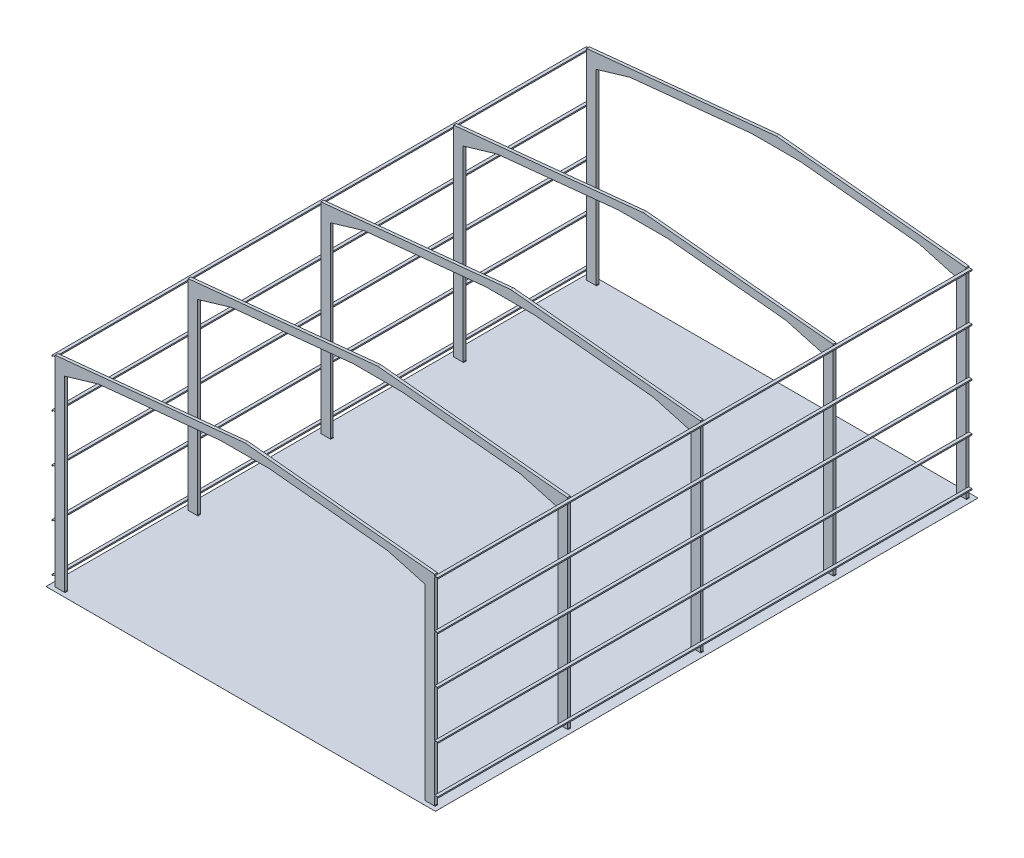
SolidWorks part; units mm, degrees
ref_plane " " through (0, 0, 0) normal (0, 0, 1) x (1, 0, 0)
ref_plane "Top Plane" through (0, 0, 0) normal (0, 1, 0) x (1, 0, 0)
ref_plane "Right Plane" through (0, 0, 0) normal (1, 0, 0) x (0, 0, -1)
sketch "Sketch1"
  dimension "D1" = 1000
  dimension "D2" = 750
  dimension "D3" = 750
  dimension "D4" = 850
  dimension "D5" = 8775
  dimension "D6" = 1300.0407
  dimension "D7" = 2150
  dimension "D8" = 500
  dimension "D9" = 2500
  dimension "D10" = 2500
  dimension "D11" = 2500
  dimension "D12" = 10600.0407
  dimension "D13" = 6000
  dimension "D14" = 7500
  dimension "D15" = 9100
  dimension "D16" = 2500
  dimension "D17" = 2500
  dimension "D18" = 100.0407
  dimension "D19" = 975
  dimension "D20" = 8000
  dimension "D21" = 400
  dimension "D22" = 1250
  dimension "D23" = 6000
  dimension "D24" = 525
  dimension "D25" = 100
  dimension "D26" = 10746.2668
  dimension "D27" = 1040.2205
  dimension "D28" = 19500
  dimension "D29" = 200
  dimension "D30" = 34.4142
  dimension "D31" = 10354.0871
  dimension "D32" = 3908.6556
  dimension "D33" = 200
  dimension "D34" = 130
  dimension "D35" = 200
  dimension "D36" = 4109.5991
  dimension "D37" = 101
sketch_block_instance "IPE500_0-1"
sketch_block "IPE500_0"
sketch_block_instance "IPE180_2-1"
sketch_block "IPE180_2"
sketch_block_instance "IPE180_3-1"
sketch_block "IPE180_3"
sketch_block_instance "Vkota-gd_4-1"
sketch_block "Vkota-gd_4"
sketch_block_instance "Vkota-gd_5-1"
sketch_block "Vkota-gd_5"
sketch_block_instance "Vkota-gd_6-1"
sketch_block "Vkota-gd_6"
sketch_block_instance "UNP160_7-1"
sketch_block "UNP160_7"
sketch_block_instance "UNP160_8-1"
sketch_block "UNP160_8"
sketch_block_instance "UNP160_9-1"
sketch_block "UNP160_9"
sketch_block_instance "UNP160_10-1"
sketch_block "UNP160_10"
sketch_block_instance "UNP300_11-1"
sketch_block "UNP300_11"
sketch_block_instance "UNP160_12-1"
sketch_block "UNP160_12"
sketch_block_instance "UNP200_13-1"
sketch_block "UNP200_13"
sketch_block_instance "UNP200_14-1"
sketch_block "UNP200_14"
sketch_block_instance "vitlo-1"
sketch_block "vitlo"
sketch_block_instance "IPE500_16-1"
sketch_block "IPE500_16"
sketch_block_instance "UNP300_17-1"
sketch_block "UNP300_17"
sketch_block_instance "IPE180_18-1"
sketch_block "IPE180_18"
sketch_block_instance "IPE180_19-1"
sketch_block "IPE180_19"
sketch_block_instance "UNP160_25-1"
sketch_block "UNP160_25"
sketch_block_instance "UNP160_26-1"
sketch_block "UNP160_26"
sketch_block_instance "UNP160_27-1"
sketch_block "UNP160_27"
sketch_block_instance "UNP160_28-1"
sketch_block "UNP160_28"
sketch_block_instance "UNP160_29-1"
sketch_block "UNP160_29"
sketch_block_instance "UNP200_32-1"
sketch_block "UNP200_32"
sketch_block_instance "UNP200_33-1"
sketch_block "UNP200_33"
sketch_block_instance "oo h-1"
sketch_block "oo h"
sketch_block_instance "A$C0EF406AC-1"
sketch_block "A$C0EF406AC"
sketch_block_instance "VISKOTA_35-1"
sketch_block "VISKOTA_35"
sketch_block_instance "VISKOTA_36-1"
sketch_block "VISKOTA_36"
sketch_block_instance "VISKOTA_37-1"
sketch_block "VISKOTA_37"
sketch_block_instance "VISKOTA_38-1"
sketch_block "VISKOTA_38"
sketch_block_instance "VISKOTA_39-1"
sketch_block "VISKOTA_39"
sketch_block_instance "VISKOTA_40-1"
sketch_block "VISKOTA_40"
sketch_block_instance "oo h_41-1"
sketch_block "oo h_41"
sketch_block_instance "VISKOTA_42-1"
sketch_block "VISKOTA_42"
sketch_block_instance "VISKOTA_43-1"
sketch_block "VISKOTA_43"
sketch_block_instance "VISKOTA_44-1"
sketch_block "VISKOTA_44"
sketch_block_instance "VISKOTA_45-1"
sketch_block "VISKOTA_45"
sketch_block_instance "VISKOTA_46-1"
sketch_block "VISKOTA_46"
sketch_block_instance "VISKOTA_47-1"
sketch_block "VISKOTA_47"
sketch_block_instance "VRATA-izgled_48-1"
sketch_block "VRATA-izgled_48"
sketch_block_instance "VISKOTA_49-1"
sketch_block "VISKOTA_49"
sketch "Sketch55" plane through (0, 0, 0) normal (0, 0, 1) x (1, 0, 0)
  line L0 (128234.4456, -80629.9544) -> (130024.2471, -80099.2286) construction
  line L1 (130024.2471, -80099.2286) -> (136434.4456, -79458.2088) construction
  line L2 (127734.4456, -79926.2138) -> (137734.4456, -78926.2138) construction
  line L3 (136434.4456, -79458.2088) -> (137734.4456, -79458.2088) construction
  line L4 (139034.4456, -79458.2088) -> (137734.4456, -79458.2088) construction
  line L5 (145244.6441, -80079.2286) -> (139034.4456, -79458.2088) construction
  line L6 (147734.4456, -79926.2138) -> (137734.4456, -78926.2138) construction
  line L7 (147234.4456, -80629.9544) -> (145244.6441, -80079.2286) construction
  line L8 (127734.4456, -90476.2544) -> (127734.4456, -79926.2138) construction
  line L9 (128234.4456, -90451.2544) -> (128234.4456, -79876.2138) construction
  line L11 (147734.4456, -90451.2544) -> (147734.4456, -79926.2138) construction
  line L12 (147234.4456, -90451.2544) -> (147234.4456, -79876.2138) construction
  line L14 (128234.4456, -80629.9544) -> (130024.2471, -80099.2286)
  line L15 (130024.2471, -80099.2286) -> (136434.4456, -79458.2088)
  line L16 (127734.4456, -79926.2138) -> (137734.4456, -78926.2138)
  line L17 (136434.4456, -79458.2088) -> (137734.4456, -79458.2088)
  line L18 (139034.4456, -79458.2088) -> (137734.4456, -79458.2088)
  line L19 (145244.6441, -80079.2286) -> (139034.4456, -79458.2088)
  line L20 (147734.4456, -79926.2138) -> (137734.4456, -78926.2138)
  line L21 (147234.4456, -80629.9544) -> (145244.6441, -80079.2286)
  line L22 (127734.4456, -90476.2544) -> (127734.4456, -79926.2138)
  line L23 (128234.4456, -90476.2544) -> (128234.4456, -80629.9544)
  line L24 (127709.4456, -90501.2544) -> (127734.4456, -90476.2544)
  line L25 (147734.4456, -90476.2544) -> (147734.4456, -79926.2138)
  line L26 (147234.4456, -90476.2544) -> (147234.4456, -80629.9544)
  line L27 (147734.4456, -90476.2544) -> (147759.4456, -90501.2544)
  line L29 (127709.4456, -90501.2544) -> (128259.4456, -90501.2544)
  line L30 (128259.4456, -90501.2544) -> (128234.4456, -90476.2544)
  line L32 (147759.4456, -90501.2544) -> (147209.4456, -90501.2544)
  line L33 (147209.4456, -90501.2544) -> (147234.4456, -90476.2544)
extrude "Extrude3" add sketch "Sketch55" along normal blind 150
sketch "Sketch56" plane through (0, 0, 0) normal (0, 0, 1) x (1, 0, 0)
  line L0 (147891.6232, -90066.2544) -> (147894.4456, -90066.2544) construction
  line L1 (147894.4456, -90501.2544) -> (147894.4456, -79768.7081) construction
  line L2 (147734.4456, -90451.2544) -> (147734.4456, -79926.2138) construction
  line L3 (147734.4456, -90066.2544) -> (147737.2681, -90066.2544) construction
  line L4 (147742.7505, -90061.193) -> (147746.1726, -90018.4171) construction
  line L5 (147882.7186, -90018.4171) -> (147886.1407, -90061.193) construction
  line L6 (147814.4456, -90008.7544) -> (147872.2521, -90008.7544) construction
  line L7 (147756.6392, -90008.7544) -> (147814.4456, -90008.7544) construction
  line L8 (147894.4456, -90001.2544) -> (147734.4456, -90001.2544) construction
  line L9 (147891.6232, -90066.2544) -> (147894.4456, -90066.2544)
  line L10 (147894.4456, -90066.2544) -> (147894.4456, -90001.2544)
  line L11 (147734.4456, -90066.2544) -> (147734.4456, -90001.2544)
  line L12 (147734.4456, -90066.2544) -> (147737.2681, -90066.2544)
  line L13 (147742.7505, -90061.193) -> (147746.1726, -90018.4171)
  line L14 (147882.7186, -90018.4171) -> (147886.1407, -90061.193)
  line L15 (147814.4456, -90008.7544) -> (147872.2521, -90008.7544)
  line L16 (147756.6392, -90008.7544) -> (147814.4456, -90008.7544)
  line L17 (147894.4456, -90001.2544) -> (147734.4456, -90001.2544)
  arc A0 (147737.2681, -90066.2544) -> (147742.7505, -90061.193) centre (147737.2681, -90060.7544) ccw construction
  arc A1 (147756.6392, -90008.7544) -> (147746.1726, -90018.4171) centre (147756.6392, -90019.2544) ccw construction
  arc A2 (147882.7186, -90018.4171) -> (147872.2521, -90008.7544) centre (147872.2521, -90019.2544) ccw construction
  arc A3 (147737.2681, -90066.2544) -> (147742.7505, -90061.193) centre (147737.2681, -90060.7544) ccw
  arc A4 (147756.6392, -90008.7544) -> (147746.1726, -90018.4171) centre (147756.6392, -90019.2544) ccw
  arc A5 (147882.7186, -90018.4171) -> (147872.2521, -90008.7544) centre (147872.2521, -90019.2544) ccw
  arc A6 (147886.1407, -90061.193) -> (147891.6232, -90066.2544) centre (147891.6232, -90060.7544) ccw construction
  arc A7 (147886.1407, -90061.193) -> (147891.6232, -90066.2544) centre (147891.6232, -90060.7544) ccw
extrude "Extrude4" add sketch "Sketch56" along normal blind 28150
pattern_linear "LPattern1" count 5 spacing 2500 along (0, 1, 0) of "Extrude4"
ref_plane "Plane2" through (137734.4456, 0, 0) normal (1, 0, 0) x (0, 0, -1)
mirror "Mirror1" about plane through (137734.4456, 0, 0) normal (1, 0, 0) of "LPattern1", "Extrude4"
pattern_linear "LPattern2" count 5 spacing 7000 along (0, 0, 1) of "Extrude3"
sketch "Sketch57" plane through (0, -90501.2544, 0) normal (0, -1, 0) x (1, 0, 0)
  line L1 (127475.8334, 28370) -> (147993.5757, 28370)
  line L2 (127475.8334, 28370) -> (127475.8334, -220)
  line L3 (127475.8334, -220) -> (147993.5757, -220)
  line L4 (147993.5757, 28370) -> (147993.5757, -220)
extrude "Extrude5" add sketch "Sketch57" against normal blind 1
